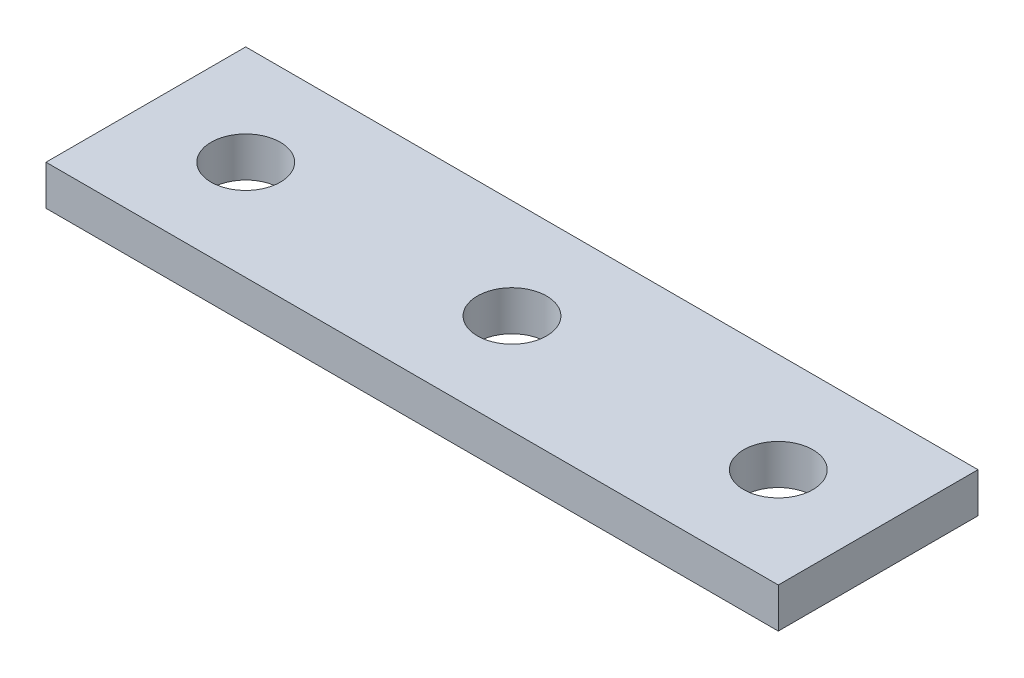
SolidWorks part; units mm, degrees
ref_plane "Спереди" through (0, 0, 0) normal (0, 0, 1) x (1, 0, 0)
ref_plane "Сверху" through (0, 0, 0) normal (0, 1, 0) x (1, 0, 0)
ref_plane "Справа" through (0, 0, 0) normal (1, 0, 0) x (0, 0, -1)
sketch "Эскиз1" plane through (0, 0, 0) normal (0, 1, 0) x (1, 0, 0)
  line L1 (-27.5, 7.5) -> (27.5, 7.5)
  line L2 (-27.5, 7.5) -> (-27.5, -7.5)
  line L3 (-27.5, -7.5) -> (27.5, -7.5)
  line L4 (27.5, 7.5) -> (27.5, -7.5)
  line L5 (-27.5, 7.5) -> (27.5, -7.5) construction
  line L6 (-27.5, -7.5) -> (27.5, 7.5) construction
  circle A0 centre (0, 0) radius 2.6
  circle A1 centre (20, 0) radius 2.6
  circle A2 centre (-20, 0) radius 2.6
  point P0 (0, 0)
extrude "Бобышка-Вытянуть1" add sketch "Эскиз1" along normal blind 3
